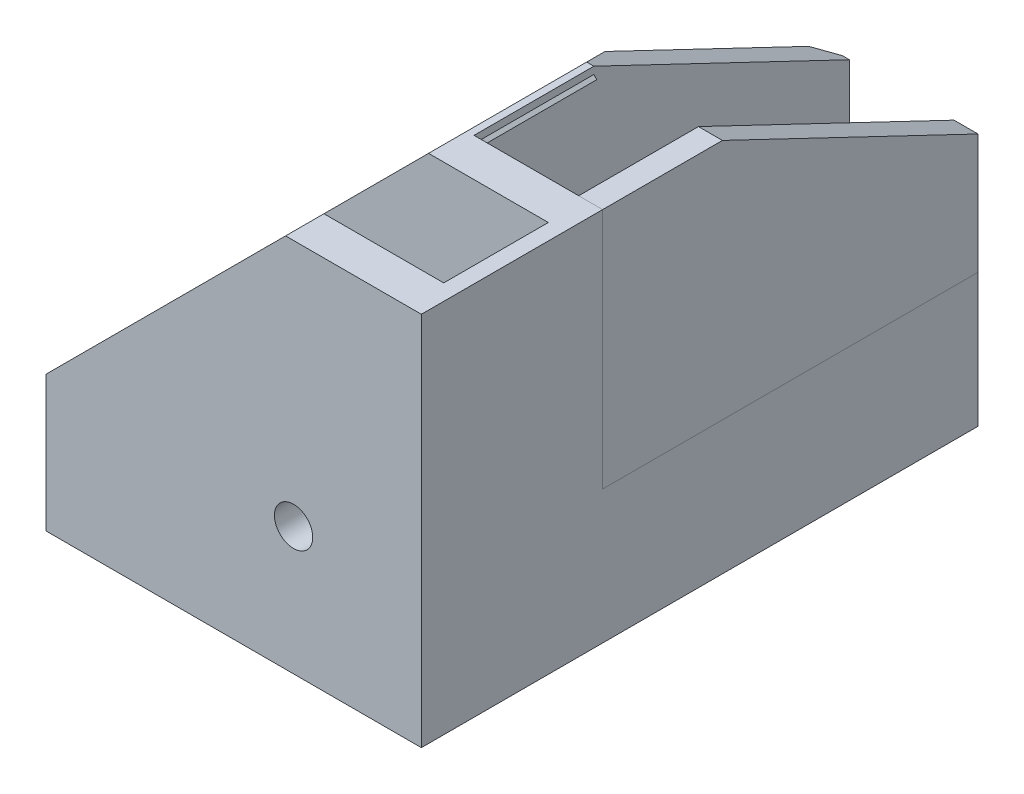
SolidWorks part; units mm, degrees
ref_plane "Front" through (0, 0, 0) normal (0, 0, 1) x (1, 0, 0)
ref_plane "Top" through (0, 0, 0) normal (0, 1, 0) x (1, 0, 0)
ref_plane "Right" through (0, 0, 0) normal (1, 0, 0) x (0, 0, -1)
other "Configuration Table"
sketch "Sketch1" plane through (0, 0, 0) normal (0, 0, 1) x (1, 0, 0)
  line L0 (0, 0) -> (0, 47)
  line L1 (0, 47) -> (-17, 47)
  line L2 (0, 0) -> (-47, 0)
  line L3 (-47, 0) -> (-47, 17)
  line L4 (-17, 47) -> (-47, 17)
extrude "Boss-Extrude1" add sketch "Sketch1" along normal mid plane 22.7
sketch "Sketch2" plane through (0, 0, 0) normal (0, 0, 1) x (1, 0, 0)
  line L0 (-47, 17) -> (-47, 2)
  line L1 (-47, 17) -> (-47, 0) construction
  line L2 (-17, 47) -> (-2, 47)
  line L3 (0, 47) -> (-17, 47) construction
  line L4 (-2, 47) -> (-2, 2)
  line L5 (-2, 2) -> (-47, 2)
  line L6 (-47, 17) -> (-17, 47)
extrude "Cut-Extrude1" cut sketch "Sketch2" against normal mid plane 13.1
sketch "Sketch3" plane through (0, 0, -11.35) normal (0, 0, -1) x (-1, 0, 0)
  line L0 (0, 0) -> (0, 2)
  line L1 (0, 0) -> (0, 47) construction
  line L2 (0, 2) -> (0, 14.7) construction
  line L4 (47, 17) -> (47, 0) construction
  line L6 (47, 0) -> (0, 0)
  line L7 (0, 14.7) -> (0, 16.7)
  line L10 (47, 16.7) -> (0, 16.7)
  line L11 (0, 14.7) -> (0, 2)
  line L12 (0, 14.7) -> (2, 14.7) construction
  line L16 (0, 8.35) -> (2, 8.35) construction
  line L17 (2, 1.8) -> (2, 14.9)
  line L18 (2, 14.9) -> (47, 14.9)
  line L19 (47, 14.9) -> (47, 16.7)
  line L20 (2, 1.8) -> (47, 1.8)
  line L21 (47, 1.8) -> (47, 0)
  point P20 (2, 8.35)
  dimension "D1" = 2
extrude "Boss-Extrude2" add sketch "Sketch3" along normal blind 47
sketch "Sketch5" plane through (0, 0, -11.35) normal (0, 0, -1) x (-1, 0, 0)
  line L0 (0, 47) -> (0, 16.7)
  line L1 (0, 16.7) -> (3, 16.7)
  line L2 (47, 16.7) -> (0, 16.7) construction
  line L3 (3, 16.7) -> (3, 47)
  line L4 (0, 47) -> (17, 47) construction
  line L5 (3, 47) -> (0, 47)
  line L6 (3, 47) -> (16.1, 47) construction
  line L7 (16.1, 47) -> (16.1, 16.7)
  line L8 (16.1, 16.7) -> (19.1, 16.7)
  line L12 (17, 47) -> (16.1, 47)
  line L13 (19.1, 16.7) -> (19.1, 44.9)
  line L14 (17, 47) -> (47, 17) construction
  line L15 (19.1, 44.9) -> (17, 47)
extrude "Boss-Extrude3" add sketch "Sketch5" along normal through all separate body
sketch "Sketch4" plane through (0, 16.7, 0) normal (0, 1, 0) x (1, 0, 0)
  line L0 (0, 58.35) -> (-17, 58.35) construction
  line L1 (-47, 58.35) -> (0, 58.35) construction
  line L2 (-47, 11.35) -> (-47, 28.35) construction
  line L3 (-47, 58.35) -> (-47, 11.35) construction
  line L4 (-17, 58.35) -> (-47, 28.35)
  line L5 (-47, 28.35) -> (-47, 58.35)
  line L6 (-47, 58.35) -> (-17, 58.35)
extrude "Cut-Extrude2" cut sketch "Sketch4" against normal through all both and the other way through all
sketch "Sketch6" plane through (0, 16.7, 0) normal (0, -1, 0) x (1, 0, 0)
  line L0 (-17, -58.35) -> (-18.7, -56.65)
  line L1 (-18.7, -58.35) -> (-18.7, -11.35) construction
  line L2 (-17, -58.35) -> (-47, -28.35) construction
  line L4 (-18.7, -58.35) -> (-17, -58.35)
  line L5 (-18.7, -58.35) -> (-19.1, -58.35)
  line L6 (-19.1, -58.35) -> (-19.1, -56.25)
  line L7 (-19.1, -58.35) -> (-19.1, -11.35) construction
  line L8 (-19.1, -56.25) -> (-18.7, -56.65)
extrude "Cut-Extrude3" cut sketch "Sketch6" against normal blind 47
sketch "Sketch7" plane through (0, 0, 0) normal (1, 0, 0) x (0, 0, -1)
  line L0 (11.35, 47) -> (26.35, 47) construction
  line L1 (58.35, 47) -> (11.35, 47) construction
  line L2 (58.35, 16.7) -> (58.35, 31.7) construction
  line L3 (58.35, 47) -> (58.35, 16.7) construction
  line L4 (58.35, 31.7) -> (26.35, 47)
  line L5 (26.35, 47) -> (58.35, 47)
  line L6 (58.35, 47) -> (58.35, 31.7)
extrude "Cut-Extrude4" cut sketch "Sketch7" against normal through all
sketch "Sketch8" plane through (0, 0, 11.35) normal (0, 0, 1) x (1, 0, 0)
  line L0 (-32, 32) -> (0, 0) construction
  line L3 (-17, 47) -> (-47, 17) construction
  circle A0 centre (-16, 16) radius 2.4
extrude "Cut-Extrude5" cut sketch "Sketch8" against normal up to next (4.8 mm away)
sketch "Sketch9" plane through (0, 2, 0) normal (0, 1, 0) x (1, 0, 0)
  line L0 (-2, -6.55) -> (-2, 6.55)
  line L1 (-2, 6.55) -> (-47, 6.55)
  line L2 (-47, 6.55) -> (-47, -6.55)
  line L3 (-47, -6.55) -> (-2, -6.55)
extrude "Cut-Extrude6" cut sketch "Sketch9" against normal up to next (2 mm away)
sketch "Sketch10" plane through (-32, 32, 0) normal (-0.7071, 0.7071, 0) x (0, 0, 1)
  line L0 (-11.35, -21.4253) -> (-6.55, -21.4253)
  line L1 (-6.55, -21.2132) -> (-6.55, -33.234) construction
  line L2 (-6.55, -21.4253) -> (-6.55, 21.2132)
  line L3 (-6.55, 21.2132) -> (-26.35, 21.2132)
  line L4 (-26.35, 21.2132) -> (-26.35, -21.4253)
  line L5 (-28.35, -21.4253) -> (-11.35, -21.4253) construction
  line L6 (-26.35, -21.4253) -> (-11.35, -21.4253)
extrude "Boss-Extrude4" add sketch "Sketch10" against normal blind 1.8
